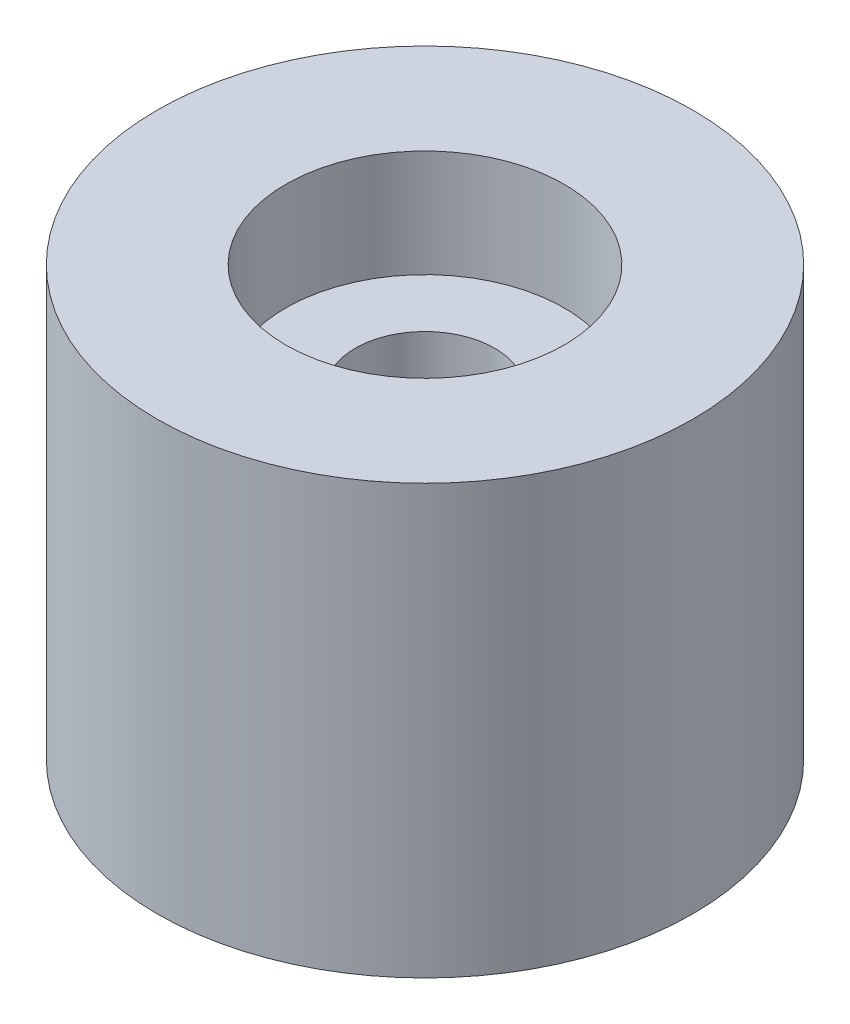
SolidWorks part; units mm, degrees
ref_plane "Front Plane" through (0, 0, 0) normal (0, 0, 1) x (1, 0, 0)
ref_plane "Top Plane" through (0, 0, 0) normal (0, 1, 0) x (1, 0, 0)
ref_plane "Right Plane" through (0, 0, 0) normal (1, 0, 0) x (0, 0, -1)
sketch "Sketch1" plane through (0, 0, 0) normal (0, 1, 0) x (1, 0, 0)
  circle A0 centre (0, 0) radius 12.5
  circle A1 centre (0, 0) radius 3.25
extrude "Boss-Extrude1" add sketch "Sketch1" along normal blind 20
sketch "Sketch2" plane through (0, 0, 0) normal (0, 1, 0) x (1, 0, 0)
  circle A0 centre (0, 0) radius 6.5
extrude "Cut-Extrude1" cut sketch "Sketch2" along normal blind 5
sketch "Sketch3" plane through (0, 20, 0) normal (0, 1, 0) x (1, 0, 0)
  circle A0 centre (0, 0) radius 6.5
extrude "Cut-Extrude2" cut sketch "Sketch3" against normal blind 5
